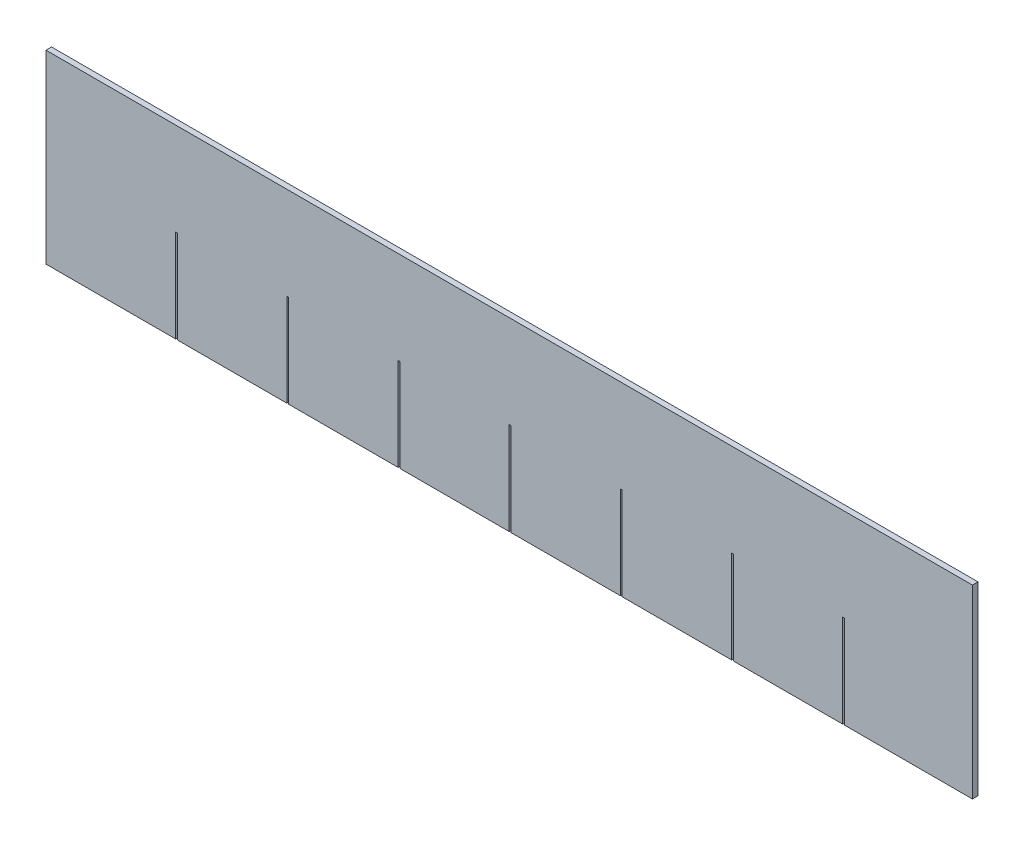
SolidWorks part; units mm, degrees
ref_plane "Front Plane" through (0, 0, 0) normal (0, 0, 1) x (1, 0, 0)
ref_plane "Top Plane" through (0, 0, 0) normal (0, 1, 0) x (1, 0, 0)
ref_plane "Right Plane" through (0, 0, 0) normal (1, 0, 0) x (0, 0, -1)
sketch "Sketch1" plane through (0, 0, 0) normal (0, 0, 1) x (1, 0, 0)
  line L1 (-31.75, 6.35) -> (31.75, 6.35)
  line L2 (-31.75, 6.35) -> (-31.75, -6.35)
  line L3 (-31.75, -6.35) -> (31.75, -6.35)
  line L4 (31.75, 6.35) -> (31.75, -6.35)
  line L5 (-31.75, 6.35) -> (31.75, -6.35) construction
  line L6 (-31.75, -6.35) -> (31.75, 6.35) construction
  point P0 (0, 0)
  dimension "D1" = 12.7
  dimension "D2" = 63.5
extrude "Boss-Extrude1" add sketch "Sketch1" along normal blind 0.381
sketch "Sketch2" plane through (0, 0, 0.381) normal (0, 0, 1) x (1, 0, 0)
  line L0 (-31.75, -6.35) -> (31.75, -6.35) construction
  line L1 (-22.86, -6.35) -> (-22.733, -6.35)
  line L2 (-22.86, -6.35) -> (-22.86, 0)
  line L3 (-22.86, 0) -> (-22.733, 0)
  line L4 (-22.733, -6.35) -> (-22.733, 0)
  line L5 (-31.75, 6.35) -> (-31.75, -6.35) construction
  line L6 (-15.24, -6.35) -> (-15.24, 0)
  line L7 (-15.113, -6.35) -> (-15.113, 0)
  line L8 (-15.24, 0) -> (-15.113, 0)
  line L9 (-15.24, -6.35) -> (-15.113, -6.35)
  line L10 (-7.62, -6.35) -> (-7.62, 0)
  line L11 (-7.493, -6.35) -> (-7.493, 0)
  line L12 (-7.62, 0) -> (-7.493, 0)
  line L13 (-7.62, -6.35) -> (-7.493, -6.35)
  line L14 (0, -6.35) -> (0, 0)
  line L15 (0.127, -6.35) -> (0.127, 0)
  line L16 (0, 0) -> (0.127, 0)
  line L17 (0, -6.35) -> (0.127, -6.35)
  line L18 (7.62, -6.35) -> (7.62, 0)
  line L19 (7.747, -6.35) -> (7.747, 0)
  line L20 (7.62, 0) -> (7.747, 0)
  line L21 (7.62, -6.35) -> (7.747, -6.35)
  line L22 (15.24, -6.35) -> (15.24, 0)
  line L23 (15.367, -6.35) -> (15.367, 0)
  line L24 (15.24, 0) -> (15.367, 0)
  line L25 (15.24, -6.35) -> (15.367, -6.35)
  line L26 (22.86, -6.35) -> (22.86, 0)
  line L27 (22.987, -6.35) -> (22.987, 0)
  line L28 (22.86, 0) -> (22.987, 0)
  line L29 (22.86, -6.35) -> (22.987, -6.35)
  dimension "D1" = 6.35
  dimension "D2" = 0.127
  dimension "D3" = 8.89
  dimension "D4" = 7
extrude "Cut-Extrude1" cut sketch "Sketch2" against normal through all
